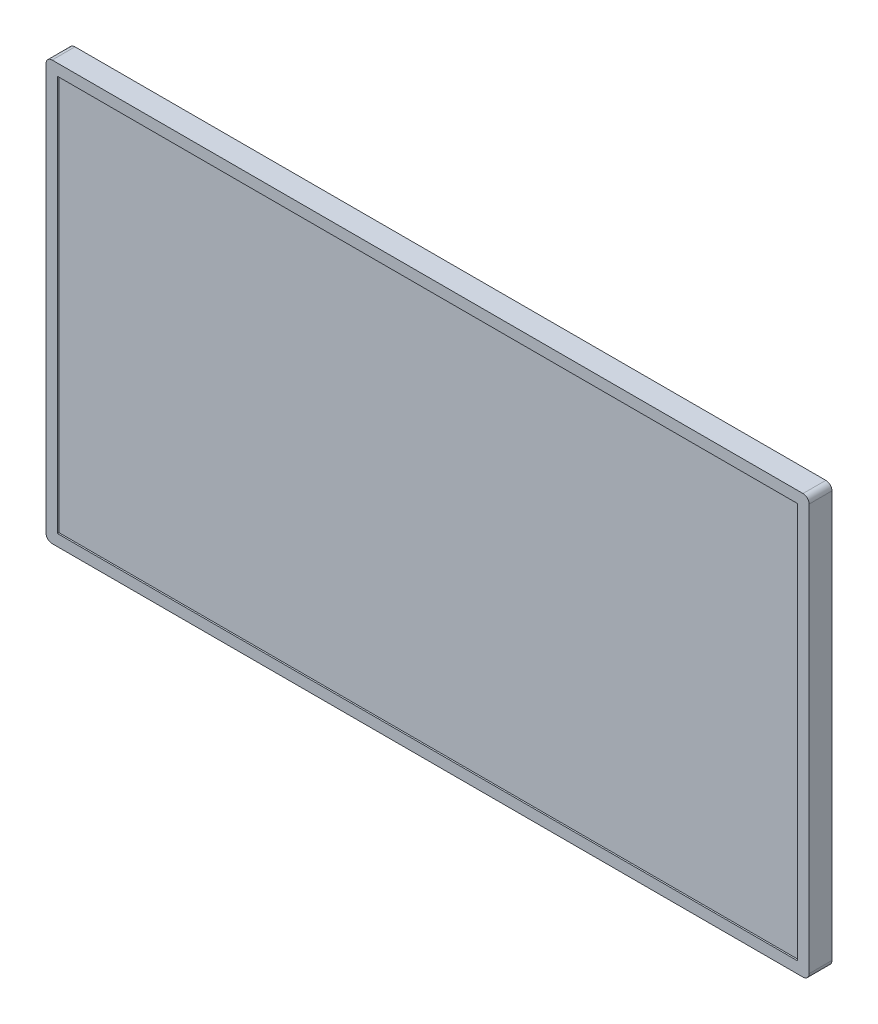
SolidWorks part; units mm, degrees
ref_plane "Alzado" through (0, 0, 0) normal (0, 0, 1) x (1, 0, 0)
ref_plane "Planta" through (0, 0, 0) normal (0, 1, 0) x (1, 0, 0)
ref_plane "Vista lateral" through (0, 0, 0) normal (1, 0, 0) x (0, 0, -1)
sketch "Croquis1" plane through (0, 0, 0) normal (0, 0, 1) x (1, 0, 0)
  line L1 (0, 0) -> (1001.9726, 0)
  line L2 (0, 0) -> (0, 550)
  line L3 (0, 550) -> (1001.9726, 550)
  line L4 (1001.9726, 0) -> (1001.9726, 550)
  dimension "D1" = 1143
  dimension "D2" = 550
  dimension "D3" = 1001.9726
extrude "Saliente-Extruir1" add sketch "Croquis1" along normal blind 30
sketch "Croquis2" plane through (0, 0, 30) normal (0, 0, 1) x (1, 0, 0)
  line L0 (500.9863, 550) -> (500.9863, 0) construction
  line L1 (1001.9726, 550) -> (0, 550) construction
  line L2 (0, 0) -> (1001.9726, 0) construction
  line L3 (1001.9726, 0) -> (1001.9726, 550) construction
  line L4 (986.9726, 15) -> (15, 15)
  line L5 (986.9726, 15) -> (986.9726, 535)
  line L6 (986.9726, 535) -> (15, 535)
  line L7 (15, 15) -> (15, 535)
  line L8 (986.9726, 15) -> (15, 535) construction
  line L9 (986.9726, 535) -> (15, 15) construction
  point P6 (500.9863, 275)
  dimension "D1" = 15
  dimension "D2" = 15
extrude "Cortar-Extruir1" cut sketch "Croquis2" against normal blind 2
fillet "Redondeo1" radius 8 4 edges at (0, 0, 15) (1001.9726, 0, 15) (1001.9726, 550, 15) (0, 550, 15)
